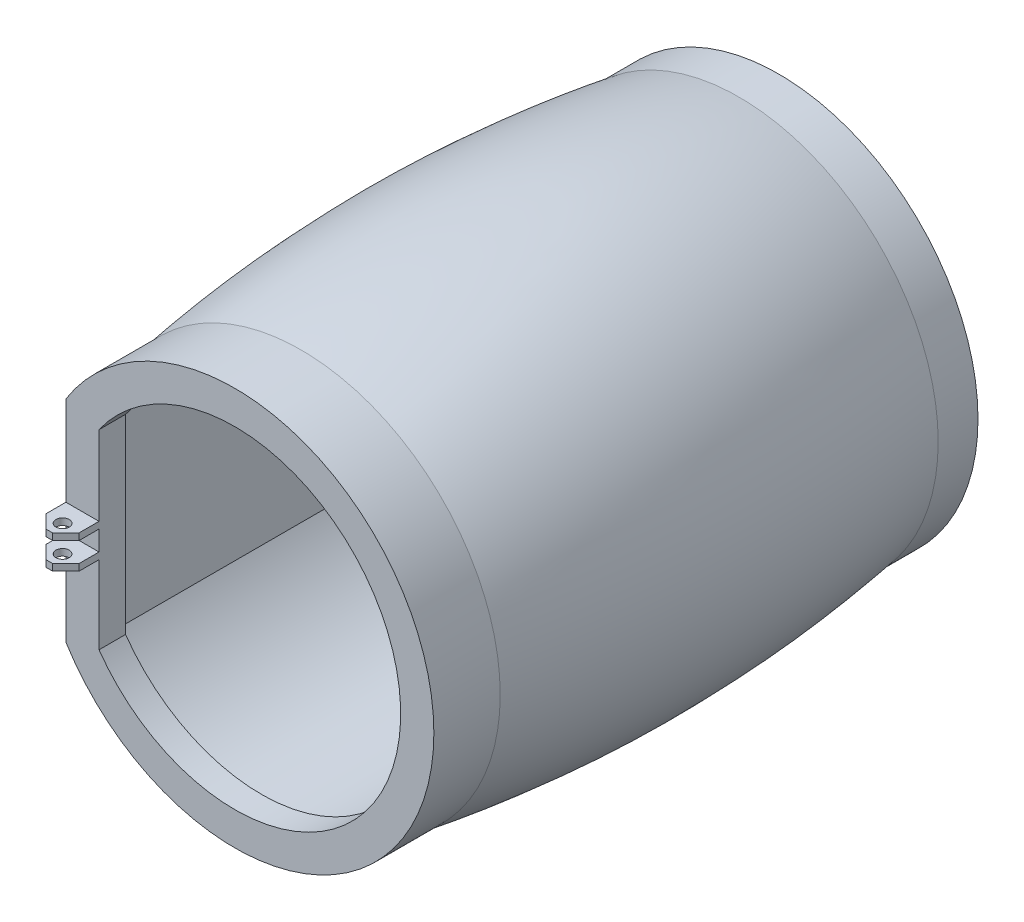
SolidWorks part; units mm, degrees
ref_plane "Front Plane" through (0, 0, 0) normal (0, 0, 1) x (1, 0, 0)
ref_plane "Top Plane" through (0, 0, 0) normal (0, 1, 0) x (1, 0, 0)
ref_plane "Right Plane" through (0, 0, 0) normal (1, 0, 0) x (0, 0, -1)
sketch "Sketch1" plane through (0, 0, 0) normal (0, 0, 1) x (1, 0, 0)
  line L0 (0, 15) -> (0, -15) construction
  line L1 (-15, 0) -> (-10.4612, 0) construction
  line L2 (-10.4612, 10.7501) -> (10.4612, 10.7501) construction
  line L3 (-10.4612, 10.7501) -> (-10.4612, -10.7501) construction
  line L4 (-10.4612, -10.7501) -> (10.4612, -10.7501) construction
  line L5 (10.4612, 10.7501) -> (10.4612, -10.7501) construction
  line L6 (-10.4612, 10.7501) -> (10.4612, -10.7501) construction
  line L7 (-10.4612, -10.7501) -> (10.4612, 10.7501) construction
  line L8 (-12.7306, -7.933) -> (-12.7306, 7.933)
  arc A0 (-12.7306, -7.933) -> (-12.7306, 7.933) centre (0, 0) ccw
  point P14 (-12.7306, 0)
  dimension "D1" = 30
  dimension "D2" = 2.2694
extrude "Boss-Extrude1" add sketch "Sketch1" along normal blind 33
sketch "Sketch2" plane through (0, 0, 33) normal (0, 0, 1) x (1, 0, 0)
  line L0 (0, 0) -> (-13.5, 0) construction
  line L1 (-11.23, 7.4925) -> (-11.23, -7.4925)
  arc A0 (-11.23, -7.4925) -> (-11.23, 7.4925) centre (0, 0) ccw
  point P3 (-11.23, 0)
  point P8 (-11.23, 0)
  dimension "D1" = 27
  dimension "D2" = 2.27
extrude "Cut-Extrude2" cut sketch "Sketch2" against normal blind 33
sketch "Sketch3" plane through (0, 0, 0) normal (0, 1, 0) x (1, 0, 0)
  line L0 (15, 0) -> (15, -33) construction
  line L1 (15, -16.5) -> (21.4054, -16.5) construction
  line L2 (15, 0) -> (15, -33)
  line L3 (0, -1000) -> (0, 49000) construction
  spline S0 degree 2 poles (15, 0) (17.6061, -16.5) (15, -33) knots 0 0 0 1 1 1
  point P4 (15, -16.5)
revolve "Revolve1" add sketch "Sketch3" angle 360 about L3
sketch "Sketch4" plane through (0, 0, 0) normal (0, 0, -1) x (-1, 0, 0)
  line L0 (12.7306, -1000) -> (12.7306, 49000) construction
  line L1 (12.7306, 7.933) -> (12.7306, -7.933) construction
  line L2 (12.7306, 16.4167) -> (12.7306, -13.1288)
  line L3 (12.7306, -13.1288) -> (18.3803, -13.1288)
  line L4 (18.3803, -13.1288) -> (18.3803, 16.8276)
  line L5 (18.3803, 16.8276) -> (12.7306, 16.4167)
  point P5 (12.7306, 0)
extrude "Cut-Extrude3" cut sketch "Sketch4" against normal blind 33
sketch "Sketch5" plane through (0, 0, 33) normal (0, 0, 1) x (1, 0, 0)
  circle A0 centre (0, 0) radius 13.5
  circle A1 centre (0, 0) radius 15
extrude "Boss-Extrude2" add sketch "Sketch5" along normal blind 3
sketch "Sketch6" plane through (0, 0, 0) normal (0, 0, -1) x (-1, 0, 0)
  circle A0 centre (0, 0) radius 15
  circle A1 centre (0, 0) radius 13.5
extrude "Boss-Extrude6" add sketch "Sketch6" along normal blind 3
sketch "Sketch7" plane through (0, 0, 0) normal (0, 0, -1) x (-1, 0, 0)
  line L0 (12.7306, 4.4925) -> (12.7306, -4.3205)
  line L1 (12.7306, 4.4925) -> (12.7306, -4.4925) construction
  circle A0 centre (0, 0) radius 13.5 construction
  spline S0 degree 2 poles (12.7306, 4.4925) (14.2662, 0.0986) (12.7306, -4.3205) knots 0 0 0 1 1 1
extrude "Boss-Extrude8" add sketch "Sketch7" against normal blind 1
sketch "Sketch8" plane through (0, 0, 33) normal (0, 0, 1) x (1, 0, 0)
  line L0 (-12.7306, 4.4925) -> (-12.7306, -4.3205)
  circle A0 centre (0, 0) radius 13.5 construction
  parabola Q0 (-12.7306, -4.3205) -> (-12.7306, 4.4925) focus (-7.1763, 0.1442) apex (-13.4979, 0.1961) construction
  spline S0 degree 3 poles (-12.7306, 4.4925) (-13.228, 3.0518) (-13.7804, 0.0574) (-13.2123, -2.9375) (-12.7306, -4.3205) knots 0 0 0 0 0.509558 1 1 1 1
extrude "Boss-Extrude9" add sketch "Sketch8" against normal blind 1
sketch "Sketch10" plane through (0, 0, -3) normal (0, 0, -1) x (-1, 0, 0)
  line L0 (12.7306, 10.1844) -> (12.7306, -10.1844)
  line L1 (12.7306, 7.933) -> (12.7306, 10.1844) construction
  line L2 (12.7306, -10.1844) -> (12.7306, -7.933) construction
  line L3 (12.7306, 10.1844) -> (17.1807, 9.4755)
  line L4 (17.1807, 9.4755) -> (17.7744, -7.9686)
  line L5 (17.7744, -7.9686) -> (12.7306, -10.1844)
  arc A0 (12.7306, 10.1844) -> (12.7306, -10.1844) centre (0, 0) ccw construction
extrude "Cut-Extrude4" cut sketch "Sketch10" against normal blind 43
sketch "Sketch12" plane through (0, 0, 33) normal (0, 0, 1) x (1, 0, 0)
  line L0 (-11.23, 7.4925) -> (-11.23, -7.4925)
  line L1 (-12.7306, 4.4925) -> (-12.7306, -4.4925)
  line L2 (-12.7306, 4.4925) -> (-12.7306, 7.4925)
  line L3 (-12.7306, 4.4925) -> (-12.7306, 7.933) construction
  line L4 (-12.7306, 7.4925) -> (-11.23, 7.4925)
  line L5 (-12.7306, -4.4925) -> (-12.7306, -7.4925)
  line L6 (-12.7306, -7.933) -> (-12.7306, -4.4925) construction
  line L7 (-12.7306, -7.4925) -> (-11.23, -7.4925)
extrude "Boss-Extrude16" add sketch "Sketch12" along normal blind 3 and the other way blind 36
sketch "Sketch13" plane through (0, 0, 36) normal (0, 0, 1) x (1, 0, 0)
  line L0 (-12.7359, 4.4773) -> (-12.7306, -4.4925)
  line L1 (-12.7306, -7.933) -> (-12.7306, 7.933) construction
  line L2 (-12.7334, -999.7033) -> (-12.7334, 49000.2967) construction
  line L3 (-12.7306, 7.933) -> (-12.7359, 4.4773)
  line L4 (-12.7306, -7.933) -> (-12.7306, -4.4925)
  arc A0 (-12.7334, -4.4844) -> (-12.7306, -4.4925) centre (0, 0) ccw
  arc A1 (-12.7334, -7.9284) -> (-12.7334, 7.9284) centre (0, 0) ccw
  arc A2 (-12.7334, 4.4844) -> (-12.7359, 4.4773) centre (0, 0) ccw
  arc M3 (-11.23, 7.4925) -> (-11.23, -7.4925) centre (0, 0) cw
  line M4 (-11.23, -7.4925) -> (-11.23, 7.4925)
  arc M5 (-12.7306, -7.933) -> (-12.7306, 7.933) centre (0, 0) ccw
  line M6 (-12.7306, 7.933) -> (-12.7306, -7.933)
extrude "Boss-Extrude18" add sketch "Sketch13" along normal blind 2 contours M6 M5 M4 M3 | M3 M4
sketch "Sketch14" plane through (0, 0, 38) normal (0, 0, 1) x (1, 0, 0)
  line L0 (-10.23, -1002.0778) -> (-10.23, 48997.9222) construction
  line L2 (-10.23, 7.1831) -> (-10.23, -7.1831)
  arc A0 (-10.23, -7.1831) -> (-10.23, 7.1831) centre (0, 0) ccw
  point P4 (-10.23, 0)
  dimension "D1" = 25
extrude "Cut-Extrude5" cut sketch "Sketch14" against normal blind 6
sketch "Sketch15" plane through (0, 0, 38) normal (0, 0, 1) x (1, 0, 0)
  line L0 (-10.23, 7.1831) -> (-10.23, -7.1831) construction
  line L1 (-12.7257, 1.1985) -> (-10.23, 1.1985)
  line L2 (-12.7257, 1.1985) -> (-12.7257, -1.3015)
  line L3 (-12.7257, -1.3015) -> (-10.23, -1.3015)
  line L4 (-10.23, 1.1985) -> (-10.23, -1.3015)
  line L5 (-12.7257, 1.1985) -> (-10.23, -1.3015) construction
  line L6 (-12.7257, -1.3015) -> (-10.23, 1.1985) construction
  point P0 (-11.4778, -0.0515)
  dimension "D1" = 2.4957
  dimension "D2" = 2.5
extrude "Boss-Extrude19" add sketch "Sketch15" along normal blind 2.5
sketch "Sketch16" plane through (0, 0, 40.5) normal (0, 0, 1) x (1, 0, 0)
  line L0 (-12.7257, -0.0515) -> (-10.23, -0.0515) construction
  line L1 (-12.7257, 1.1985) -> (-12.7257, -1.3015) construction
  line L2 (-10.23, -1.3015) -> (-10.23, 1.1985) construction
  line L3 (-10.23, 1.1985) -> (-12.7281, 1.1985) construction
  line L4 (-12.7257, 0.6985) -> (-10.23, 0.6985)
  line L5 (-12.7257, 0.6985) -> (-12.7257, -0.8015)
  line L6 (-12.7257, -0.8015) -> (-10.23, -0.8015)
  line L7 (-10.23, 0.6985) -> (-10.23, -0.8015)
  line L8 (-12.7257, 0.6985) -> (-10.23, -0.8015) construction
  line L9 (-12.7257, -0.8015) -> (-10.23, 0.6985) construction
  point P6 (-11.4778, -0.0515)
  dimension "D1" = 0.5
extrude "Cut-Extrude6" cut sketch "Sketch16" against normal blind 2.5
sketch "Sketch17" plane through (0, -1.3015, 0) normal (0, -1, 0) x (1, 0, 0)
  line L0 (-12.7257, 40.5) -> (-10.23, 40.5) construction
  line L1 (-11.4778, -959.5) -> (-11.4778, 49040.5) construction
  line L2 (-12.7281, 38) -> (-10.23, 38) construction
  line L3 (-10.23, 40.5) -> (-10.23, 38) construction
  circle A0 centre (-11.4778, 39.5) radius 0.5
  point P7 (-11.4778, 40.5)
  dimension "D1" = 1.5
  dimension "D3" = 1
  dimension "D2" = 1.2478
extrude "Cut-Extrude7" cut sketch "Sketch17" against normal blind 2.5
chamfer "Chamfer1" distance 1 angle 45 4 edges at (-12.7257, -1.0515, 40.5) (-12.7257, 0.9485, 40.5) (-10.23, -1.0515, 40.5) (-10.23, 0.9485, 40.5)
